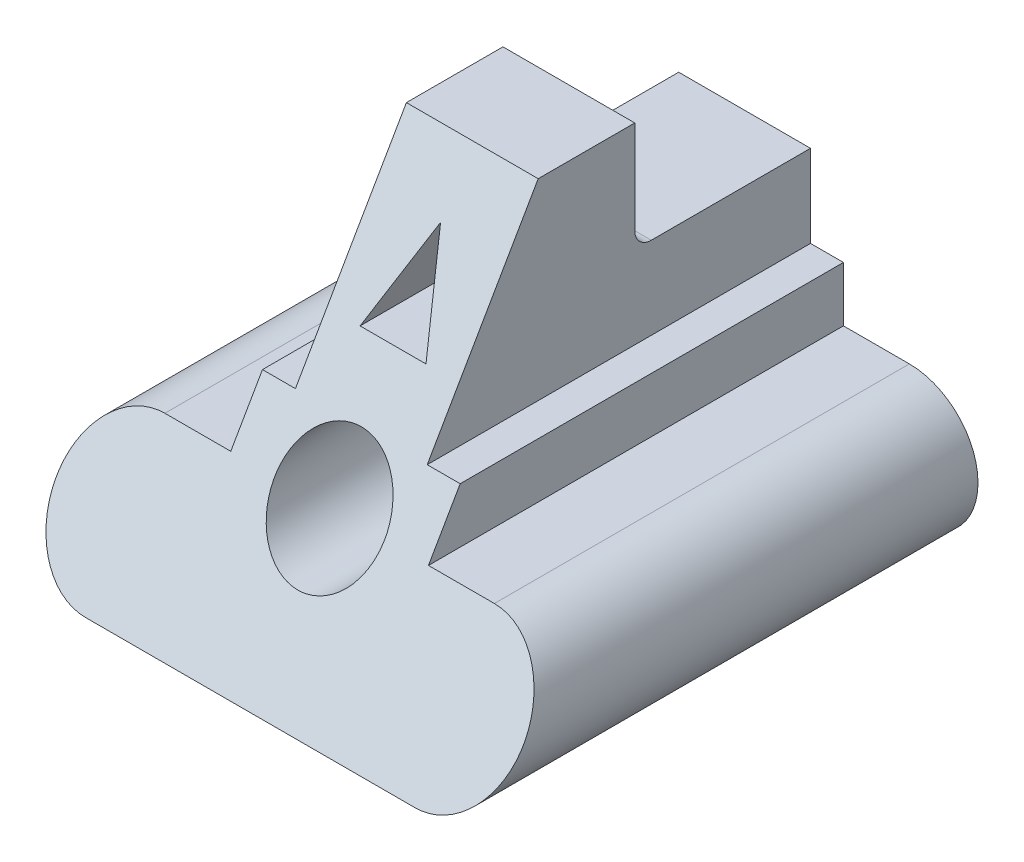
SolidWorks part; units mm, degrees
material "6061 Alloy"
ref_plane "Front Plane" through (0, 0, 0) normal (0, 0, 1) x (1, 0, 0)
ref_plane "Top Plane" through (0, 0, 0) normal (0, 1, 0) x (1, 0, 0)
ref_plane "Right Plane" through (0, 0, 0) normal (1, 0, 0) x (0, 0, -1)
sketch "Sketch1" plane through (0, 0, 0) normal (0, 0, 1) x (1, 0, 0)
  line L0 (-30, 0) -> (30, 0) construction
  line L1 (-30, 12.5) -> (-18, 12.5)
  line L2 (-30, -12.5) -> (30, -12.5)
  line L3 (-18, 12.5) -> (-18, 22.5)
  line L4 (-18, 22.5) -> (-12, 22.5)
  line L5 (18, 22.5) -> (18, 12.5)
  line L6 (18, 12.5) -> (30, 12.5)
  line L7 (-12, 22.5) -> (-12, 57.5)
  line L8 (-12, 57.5) -> (12, 57.5)
  line L9 (12, 57.5) -> (12, 22.5)
  line L10 (12, 22.5) -> (18, 22.5)
  arc A0 (-30, 12.5) -> (-30, -12.5) centre (-30, 0) ccw
  arc A1 (30, -12.5) -> (30, 12.5) centre (30, 0) ccw
  circle A2 centre (0, 12.5) radius 10
  point P3 (0, -12.5)
  point P8 (0, 57.5)
  point P15 (0, 0)
  dimension "D1" = 60
  dimension "D2" = 12.5
  dimension "D3" = 10
  dimension "D8" = 20
  dimension "D9" = 12.5
  dimension "D4" = 12
  dimension "D5" = 35
  dimension "D6" = 6
  dimension "D7" = 6
  dimension "D10" = 12
  dimension "D11" = 10
  dimension "D12" = 24
  dimension "D13" = 70
extrude "Boss-Extrude1" add sketch "Sketch1" against normal blind 90
sketch "Sketch2" plane through (12, 0, 0) normal (1, 0, 0) x (0, 0, -1)
  line L0 (90, 57.5) -> (0, 57.5) construction
  line L1 (58, 57.5) -> (90, 57.5)
  line L2 (58, 57.5) -> (58, 37.5)
  line L3 (58, 37.5) -> (90, 37.5)
  line L4 (90, 57.5) -> (90, 37.5)
  line L5 (90, 22.5) -> (90, 57.5) construction
  dimension "D1" = 20
  dimension "D2" = 32
extrude "Cut-Extrude1" cut sketch "Sketch2" against normal blind 30
fillet "Fillet1" radius 3 1 edges at (0, 37.5, -58)
sketch "Sketch3" plane through (0, 0, 0) normal (0, 0, 1) x (1, 0, 0)
  line L0 (0, 47.5) -> (-6, 32.5)
  line L1 (-6, 32.5) -> (6, 32.5)
  line L2 (6, 32.5) -> (0, 47.5)
  line L3 (-30, -12.5) -> (30, -12.5) construction
  point P2 (0, 32.5)
  dimension "D1" = 12
  dimension "D2" = 45
  dimension "D3" = 15
extrude "Cut-Extrude2" cut sketch "Sketch3" against normal blind 55
ref_plane "Plane1" through (0, -3.125, -5.4127) normal (0, 0.5, 0.866) x (1, 0, 0)
sketch "Sketch6" plane through (0, -3.125, -5.4127) normal (0, 0.5, 0.866) x (1, 0, 0)
  line L1 (-45.2119, -13.0918) -> (48.3536, -13.0918)
  line L2 (-45.2119, -13.0918) -> (-45.2119, 78.8857)
  line L3 (-45.2119, 78.8857) -> (48.3536, 78.8857)
  line L4 (48.3536, -13.0918) -> (48.3536, 78.8857)
  dimension "D1" = 91.9775
  dimension "D2" = 93.5655
extrude "Cut-Extrude3" cut sketch "Sketch6" along normal blind 55
